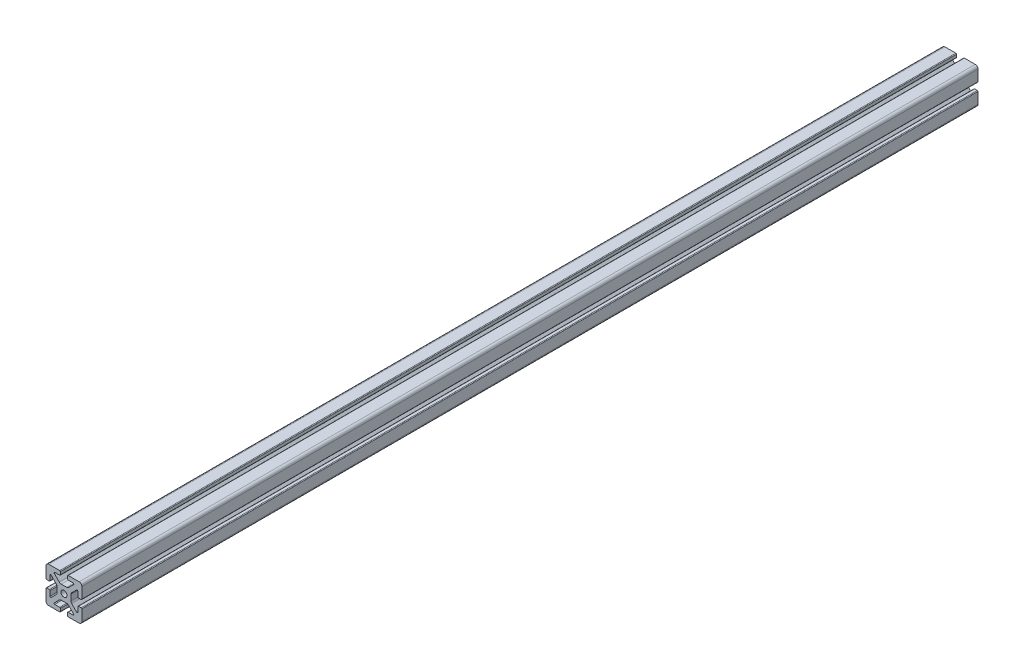
SolidWorks part; units mm, degrees
ref_plane "Front Plane" through (0, 0, 0) normal (0, 0, 1) x (1, 0, 0)
ref_plane "Top Plane" through (0, 0, 0) normal (0, 1, 0) x (1, 0, 0)
ref_plane "Right Plane" through (0, 0, 0) normal (1, 0, 0) x (0, 0, -1)
sketch "Sketch1" plane through (0, 0, 0) normal (0, 0, 1) x (1, 0, 0)
  line L2 (-20, 16.952) -> (-20, 4.7625)
  line L3 (-16.952, 20) -> (-4.7625, 20)
  line L4 (-4.0005, 19.238) -> (-4.0005, 16.2662)
  line L5 (-4.7625, 15.5042) -> (-10.2235, 15.5042)
  line L6 (-10.7623, 14.2034) -> (-5.194, 8.6351)
  line L7 (-14.2034, 10.7623) -> (-8.6351, 5.194)
  line L8 (-15.5042, 10.2235) -> (-15.5042, 4.7625)
  line L9 (-16.2662, 4.0005) -> (-19.238, 4.0005)
  line L11 (-3.0746, 7.7572) -> (3.0746, 7.7572)
  line L12 (-7.7572, 3.0746) -> (-7.7572, -3.0746)
  line L13 (16.2662, 4.0005) -> (19.238, 4.0005)
  line L14 (15.5042, 10.2235) -> (15.5042, 4.7625)
  line L15 (20, 16.952) -> (20, 4.7625)
  line L16 (16.952, 20) -> (4.7625, 20)
  line L17 (4.0005, 19.238) -> (4.0005, 16.2662)
  line L18 (4.7625, 15.5042) -> (10.2235, 15.5042)
  line L19 (7.7572, 3.0746) -> (7.7572, -3.0746)
  line L20 (10.7623, 14.2034) -> (5.194, 8.6351)
  line L21 (14.2034, 10.7623) -> (8.6351, 5.194)
  line L22 (-16.2662, -4.0005) -> (-19.238, -4.0005)
  line L23 (-15.5042, -10.2235) -> (-15.5042, -4.7625)
  line L24 (-14.2034, -10.7623) -> (-8.6351, -5.194)
  line L25 (-10.7623, -14.2034) -> (-5.194, -8.6351)
  line L26 (-4.7625, -15.5042) -> (-10.2235, -15.5042)
  line L27 (-4.0005, -19.238) -> (-4.0005, -16.2662)
  line L28 (-16.952, -20) -> (-4.7625, -20)
  line L29 (-20, -16.952) -> (-20, -4.7625)
  line L30 (20, -16.952) -> (20, -4.7625)
  line L31 (16.952, -20) -> (4.7625, -20)
  line L32 (4.0005, -19.238) -> (4.0005, -16.2662)
  line L33 (4.7625, -15.5042) -> (10.2235, -15.5042)
  line L34 (10.7623, -14.2034) -> (5.194, -8.6351)
  line L35 (14.2034, -10.7623) -> (8.6351, -5.194)
  line L36 (15.5042, -10.2235) -> (15.5042, -4.7625)
  line L37 (16.2662, -4.0005) -> (19.238, -4.0005)
  line L38 (-3.0746, -7.7572) -> (3.0746, -7.7572)
  circle A0 centre (0, 0) radius 3.4036
  arc A1 (-20, 16.952) -> (-16.952, 20) centre (-16.952, 16.952) cw
  arc A2 (-14.2034, 10.7623) -> (-15.5042, 10.2235) centre (-14.7422, 10.2235) ccw
  arc A3 (-10.2235, 15.5042) -> (-10.7623, 14.2034) centre (-10.2235, 14.7422) ccw
  arc A4 (-4.7625, 20) -> (-4.0005, 19.238) centre (-4.7625, 19.238) cw
  arc A5 (-20, 4.7625) -> (-19.238, 4.0005) centre (-19.238, 4.7625) ccw
  arc A6 (-15.5042, 4.7625) -> (-16.2662, 4.0005) centre (-16.2662, 4.7625) cw
  arc A7 (-4.0005, 16.2662) -> (-4.7625, 15.5042) centre (-4.7625, 16.2662) cw
  arc A8 (-3.0746, 7.7572) -> (-5.194, 8.6351) centre (-3.0746, 10.7544) cw
  arc A9 (-7.7572, 3.0746) -> (-8.6351, 5.194) centre (-10.7544, 3.0746) ccw
  arc A10 (15.5042, 4.7625) -> (16.2662, 4.0005) centre (16.2662, 4.7625) ccw
  arc A11 (20, 4.7625) -> (19.238, 4.0005) centre (19.238, 4.7625) cw
  arc A12 (20, 16.952) -> (16.952, 20) centre (16.952, 16.952) ccw
  arc A13 (4.7625, 20) -> (4.0005, 19.238) centre (4.7625, 19.238) ccw
  arc A14 (4.0005, 16.2662) -> (4.7625, 15.5042) centre (4.7625, 16.2662) ccw
  arc A15 (3.0746, 7.7572) -> (5.194, 8.6351) centre (3.0746, 10.7544) ccw
  arc A16 (7.7572, 3.0746) -> (8.6351, 5.194) centre (10.7544, 3.0746) cw
  arc A17 (14.2034, 10.7623) -> (15.5042, 10.2235) centre (14.7422, 10.2235) cw
  arc A18 (10.2235, 15.5042) -> (10.7623, 14.2034) centre (10.2235, 14.7422) cw
  arc A19 (-7.7572, -3.0746) -> (-8.6351, -5.194) centre (-10.7544, -3.0746) cw
  arc A20 (-3.0746, -7.7572) -> (-5.194, -8.6351) centre (-3.0746, -10.7544) ccw
  arc A21 (-4.0005, -16.2662) -> (-4.7625, -15.5042) centre (-4.7625, -16.2662) ccw
  arc A22 (-15.5042, -4.7625) -> (-16.2662, -4.0005) centre (-16.2662, -4.7625) ccw
  arc A23 (-20, -4.7625) -> (-19.238, -4.0005) centre (-19.238, -4.7625) cw
  arc A24 (-4.7625, -20) -> (-4.0005, -19.238) centre (-4.7625, -19.238) ccw
  arc A25 (-10.2235, -15.5042) -> (-10.7623, -14.2034) centre (-10.2235, -14.7422) cw
  arc A26 (-14.2034, -10.7623) -> (-15.5042, -10.2235) centre (-14.7422, -10.2235) cw
  arc A27 (-20, -16.952) -> (-16.952, -20) centre (-16.952, -16.952) ccw
  arc A28 (20, -16.952) -> (16.952, -20) centre (16.952, -16.952) cw
  arc A29 (14.2034, -10.7623) -> (15.5042, -10.2235) centre (14.7422, -10.2235) ccw
  arc A30 (10.2235, -15.5042) -> (10.7623, -14.2034) centre (10.2235, -14.7422) ccw
  arc A31 (4.7625, -20) -> (4.0005, -19.238) centre (4.7625, -19.238) cw
  arc A32 (20, -4.7625) -> (19.238, -4.0005) centre (19.238, -4.7625) ccw
  arc A33 (15.5042, -4.7625) -> (16.2662, -4.0005) centre (16.2662, -4.7625) cw
  arc A34 (4.0005, -16.2662) -> (4.7625, -15.5042) centre (4.7625, -16.2662) cw
  arc A35 (3.0746, -7.7572) -> (5.194, -8.6351) centre (3.0746, -10.7544) cw
  arc A36 (7.7572, -3.0746) -> (8.6351, -5.194) centre (10.7544, -3.0746) ccw
extrude "Boss-Extrude1" add sketch "Sketch1" along normal mid plane 1000
